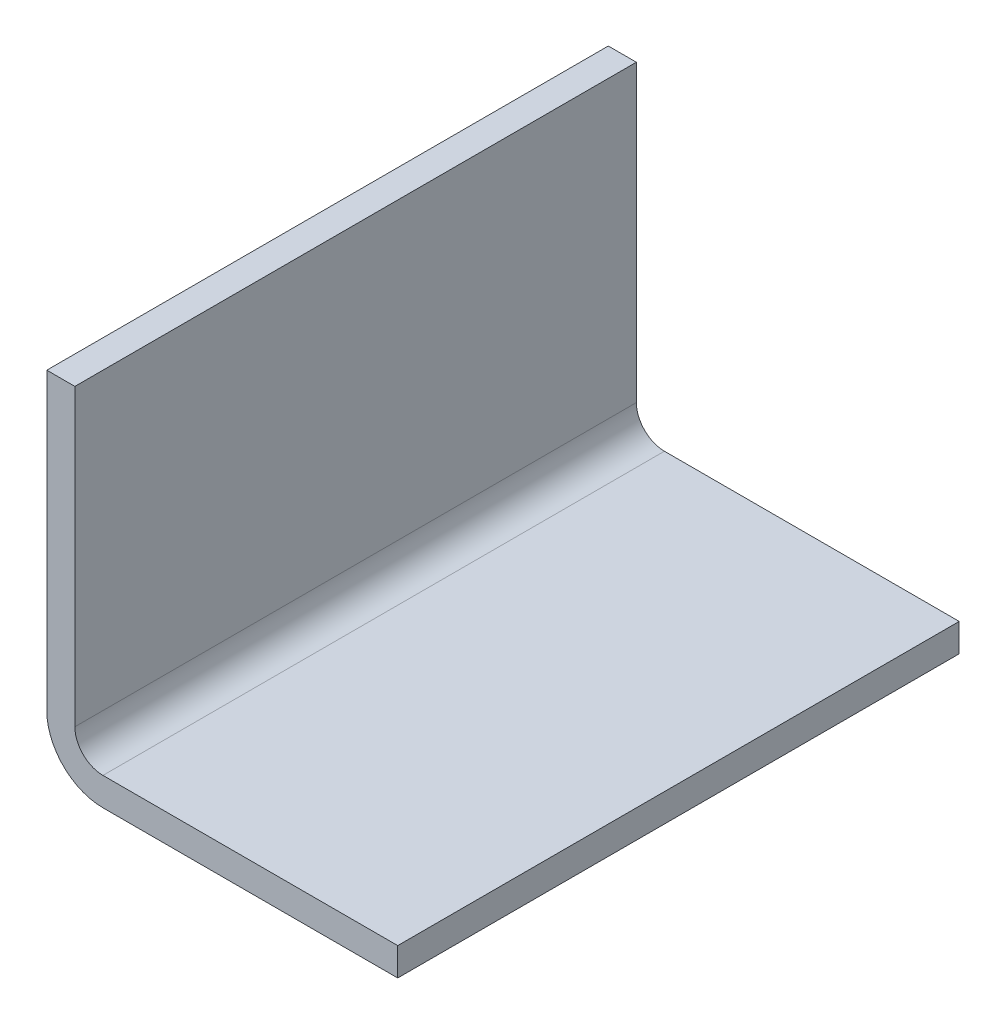
SolidWorks part; units mm, degrees
ref_plane "Front Plane" through (0, 0, 0) normal (0, 0, 1) x (1, 0, 0)
ref_plane "Top Plane" through (0, 0, 0) normal (0, 1, 0) x (1, 0, 0)
ref_plane "Right Plane" through (0, 0, 0) normal (1, 0, 0) x (0, 0, -1)
sketch "Sketch1" plane through (0, 0, 0) normal (0, 0, 1) x (1, 0, 0)
  line L0 (0, 4) -> (0, 25)
  line L1 (0, 25) -> (2, 25)
  line L2 (2, 25) -> (2, 4)
  line L3 (4, 2) -> (25, 2)
  line L4 (25, 2) -> (25, 0)
  line L5 (25, 0) -> (4, 0)
  arc A0 (2, 4) -> (4, 2) centre (4, 4) ccw
  arc A1 (0, 4) -> (4, 0) centre (4, 4) ccw
  point P11 (0, 0)
  dimension "D5" = 2
  dimension "D6" = 4
  dimension "D1" = 25
  dimension "D2" = 25
  dimension "D3" = 2
  dimension "D4" = 2
extrude "Boss-Extrude1" add sketch "Sketch1" along normal mid plane 40
